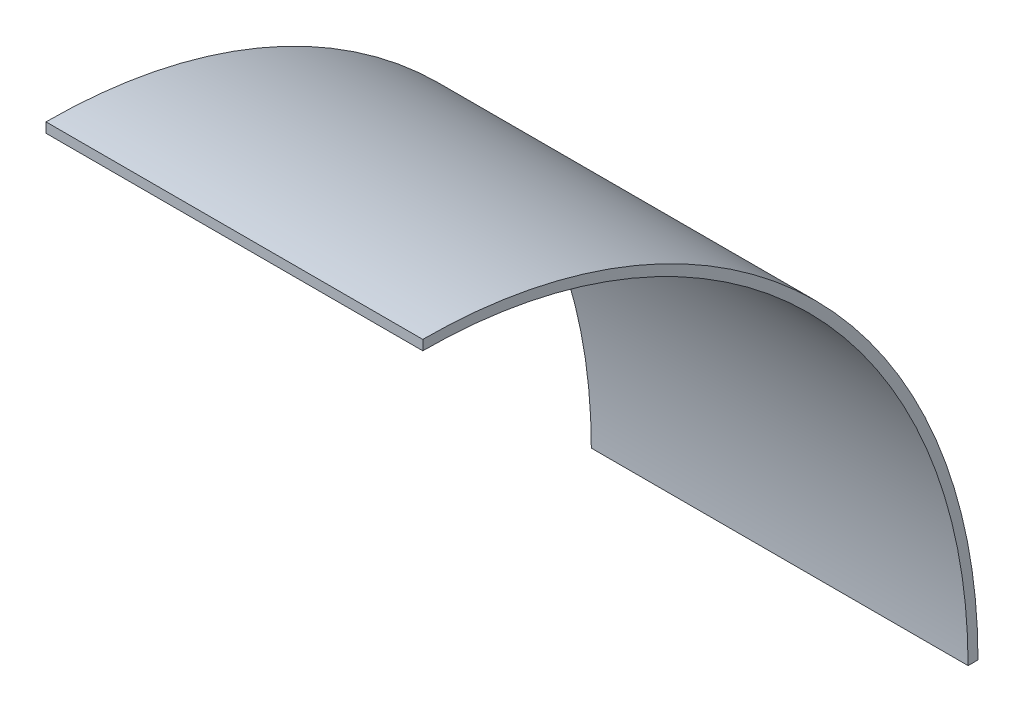
SolidWorks part; units mm, degrees
ref_plane "Front" through (0, 0, 0) normal (0, 0, 1) x (1, 0, 0)
ref_plane "Top" through (0, 0, 0) normal (0, 1, 0) x (1, 0, 0)
ref_plane "Right" through (0, 0, 0) normal (1, 0, 0) x (0, 0, -1)
sketch "Sketch1" plane through (0, 0, 0) normal (1, 0, 0) x (0, 0, -1)
  line L1 (0, 174.625) -> (0, 177.8)
  line L2 (174.625, 0) -> (177.8, 0)
  arc A0 (177.8, 0) -> (0, 177.8) centre (0, 0) ccw
  arc A1 (174.625, 0) -> (0, 174.625) centre (0, 0) ccw
  dimension "D1" = 355.6
  dimension "D2" = 3.175
extrude "Boss-Extrude1" add sketch "Sketch1" along normal blind 120.65
